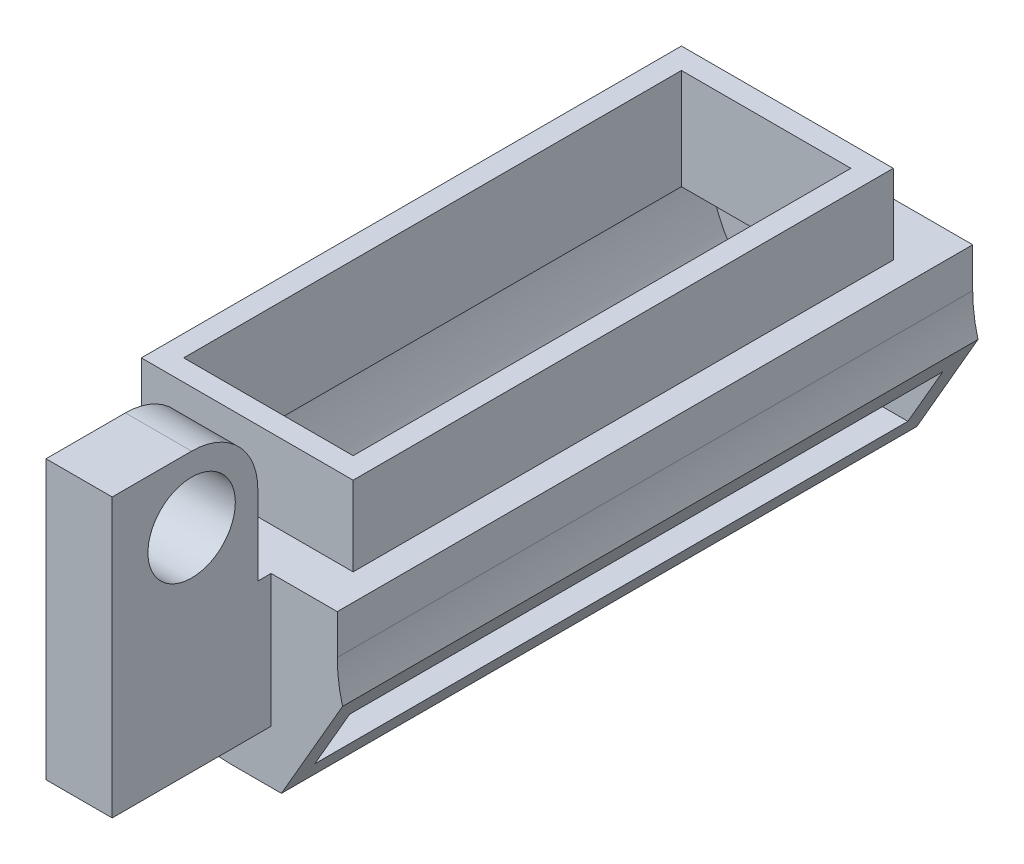
SolidWorks part; units mm, degrees
ref_plane "Plano frontal" through (0, 0, 0) normal (0, 0, 1) x (1, 0, 0)
ref_plane "Plano superior" through (0, 0, 0) normal (0, 1, 0) x (1, 0, 0)
ref_plane "Plano direito" through (0, 0, 0) normal (1, 0, 0) x (0, 0, -1)
sketch "Esboço1" plane through (0, 0, 0) normal (0, 0, 1) x (1, 0, 0)
  line L0 (-5, 0) -> (5, 0)
  line L2 (5.2, -3) -> (2.8906, -7)
  line L3 (2.8906, -7) -> (1, -7)
  line L4 (-5, -1) -> (-5, 0)
  line L5 (5, -1.5) -> (5, 0)
  arc A0 (5, -1.5) -> (5.2, -3) centre (10.725, -1.5) ccw
  arc A1 (1, -7) -> (-5, -1) centre (1, -1) cw
  point P3 (6.2983, -0.4143)
  point P4 (0, 0)
  point P6 (4.6969, -1.7602)
  point P12 (5, -0.1076)
  point P13 (6.2983, -5)
  point P14 (5, -2.1861)
  point P15 (5, -2.5779)
  dimension "D5" = 6
  dimension "D1" = 7
  dimension "D2" = 10
  dimension "D3" = 60
  dimension "D4" = 4
  dimension "D6" = 0.2
  dimension "D7" = 1.5
extrude "Ressalto-extrusão1" add sketch "Esboço1" along normal mid plane 24
sketch "Esboço4" plane through (0, 0, 0) normal (0, 1, 0) x (1, 0, 0)
  line L0 (5, 12) -> (-5, 12) construction
  line L1 (-4, -10.4) -> (4, -10.4)
  line L2 (-4, -10.4) -> (-4, 10)
  line L3 (-4, 10) -> (4, 10)
  line L4 (4, -10.4) -> (4, 10)
  line L5 (-4, -10.4) -> (4, 10) construction
  line L6 (-4, 10) -> (4, -10.4) construction
  point P0 (0, -0.2)
  point P5 (0, 0)
  point P7 (0, -1.1565)
  dimension "D1" = 20.4
  dimension "D2" = 8
  dimension "D3" = 2
extrude "Ressalto-extrusão2" add sketch "Esboço4" along normal blind 3
shell "Casca2" thickness 0.8
sketch "Esboço5" plane through (0, 0, 0) normal (1, 0, 0) x (0, 0, -1)
  line L0 (-12, 0) -> (-12.5, 0)
  line L1 (-12.5, 0) -> (-12.5, 3)
  line L2 (-15, 5.5) -> (-18, 5.5)
  line L3 (-18, 5.5) -> (-18, -5)
  line L4 (-18, -5) -> (-12, -5)
  line L5 (-12, -1) -> (-12, -7) construction
  line L6 (-12, -5) -> (-12, 0)
  line L7 (12, -7) -> (12, -1) construction
  line L8 (-12, 0) -> (12, 0) construction
  circle A0 centre (-15, 3) radius 1.65
  arc A2 (-12.5, 3) -> (-15, 5.5) centre (-15, 3) ccw
  point P6 (-18, 5.5)
  point P16 (-15.25, 2.3442)
  point P17 (0, 0)
  point P18 (-18, 5.3608)
  point P23 (-15.25, 1.9966)
  point P24 (0, 0)
  dimension "D5" = 3.3
  dimension "D6" = 2.5
  dimension "D1" = 5
  dimension "D2" = 0.5
  dimension "D3" = 30
  dimension "D4" = 5.5
  dimension "D7" = 3
  dimension "D8" = 3
extrude "Ressalto-extrusão3" add sketch "Esboço5" along normal blind 2.5
